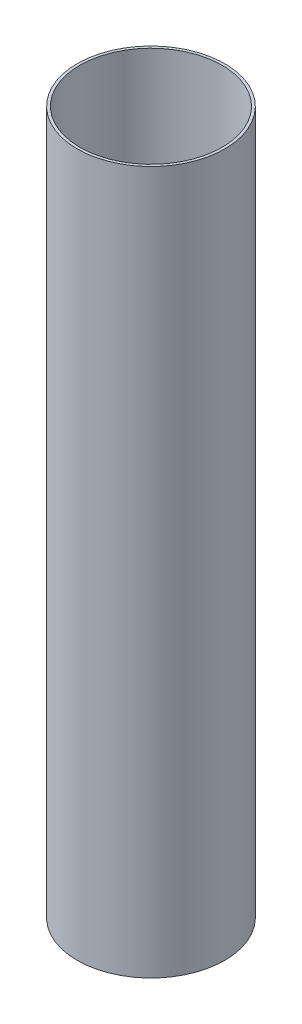
SolidWorks part; units mm, degrees
material "Corrugated Paper"
ref_plane "Front Plane" through (0, 0, 0) normal (0, 0, 1) x (1, 0, 0)
ref_plane "Top Plane" through (0, 0, 0) normal (0, 1, 0) x (1, 0, 0)
ref_plane "Right Plane" through (0, 0, 0) normal (1, 0, 0) x (0, 0, -1)
sketch "Sketch1" plane through (0, 0, 0) normal (0, 1, 0) x (1, 0, 0)
  circle A0 centre (0, 0) radius 12
  dimension "D1" = 24
extrude "Boss-Extrude1" add sketch "Sketch1" along normal blind 114.25
sketch "Sketch2" plane through (0, 114.25, 0) normal (0, 1, 0) x (1, 0, 0)
  circle A0 centre (0, 0) radius 11.565
  dimension "D1" = 23.13
extrude "Cut-Extrude1" cut sketch "Sketch2" against normal blind 40
sketch "Sketch3" plane through (0, 0, 0) normal (0, -1, 0) x (1, 0, 0)
  circle A0 centre (0, 0) radius 3.3
  dimension "D1" = 6.6
extrude "Cut-Extrude2" cut sketch "Sketch3" against normal through all both and the other way through all
